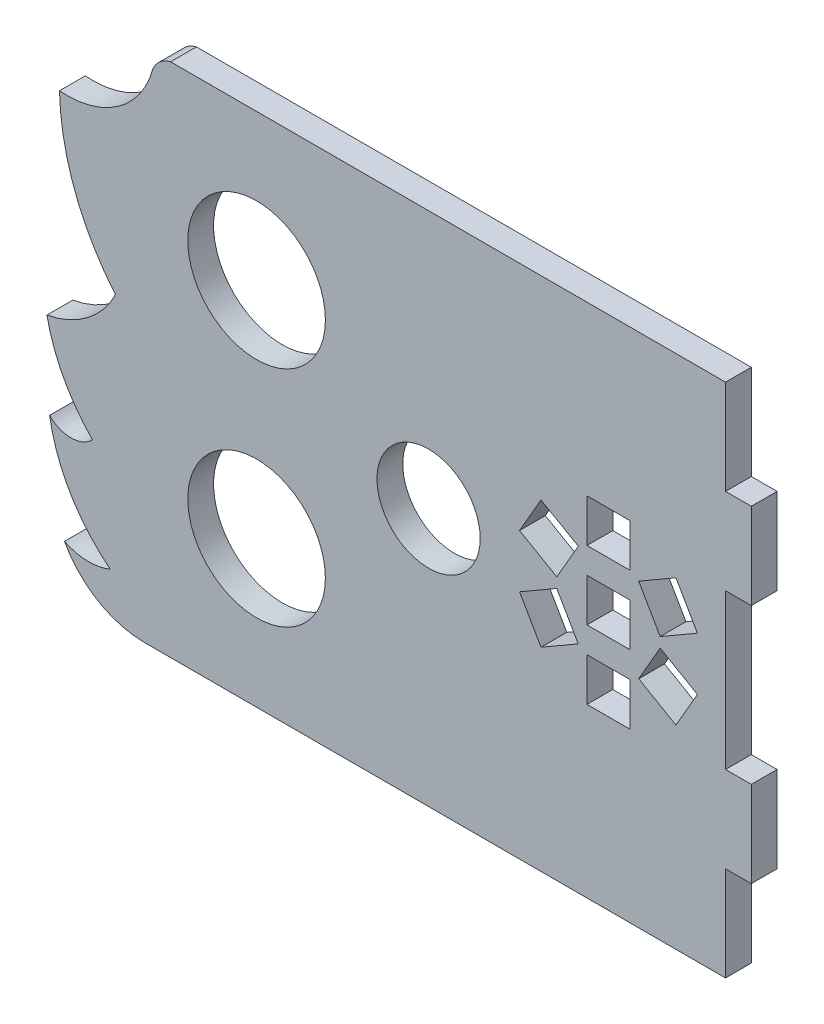
SolidWorks part; units mm, degrees
ref_plane "Alzado" through (0, 0, 0) normal (0, 0, 1) x (1, 0, 0)
ref_plane "Planta" through (0, 0, 0) normal (0, 1, 0) x (1, 0, 0)
ref_plane "Vista lateral" through (0, 0, 0) normal (1, 0, 0) x (0, 0, -1)
sketch "Model" plane through (0, 0, 0) normal (0, 0, 1) x (1, 0, 0)
  line L0 (76.3477, 34.88) -> (76.3477, 24.88)
  line L1 (76.3477, 6.88) -> (76.3477, -3.12)
  line L2 (53.7254, 16.4649) -> (56.2254, 20.7951)
  line L3 (49.3953, 18.9649) -> (53.7254, 16.4649)
  line L4 (51.8953, 23.2951) -> (49.3953, 18.9649)
  line L5 (56.2254, 20.7951) -> (51.8953, 23.2951)
  line L6 (49.3953, 12.7951) -> (51.8953, 8.4649)
  line L7 (53.7254, 15.2951) -> (49.3953, 12.7951)
  line L8 (56.2254, 10.9649) -> (53.7254, 15.2951)
  line L9 (51.8953, 8.4649) -> (56.2254, 10.9649)
  line L10 (62.2386, 26.38) -> (57.2386, 26.38)
  line L11 (62.2386, 21.38) -> (62.2386, 26.38)
  line L12 (57.2386, 21.38) -> (62.2386, 21.38)
  line L13 (57.2386, 26.38) -> (57.2386, 21.38)
  line L14 (65.7517, 15.2951) -> (63.2517, 10.9649)
  line L15 (70.0818, 12.7951) -> (65.7517, 15.2951)
  line L16 (67.5818, 8.4649) -> (70.0818, 12.7951)
  line L17 (63.2517, 10.9649) -> (67.5818, 8.4649)
  line L18 (70.0818, 18.9649) -> (67.5818, 23.2951)
  line L19 (65.7517, 16.4649) -> (70.0818, 18.9649)
  line L20 (63.2517, 20.7951) -> (65.7517, 16.4649)
  line L21 (67.5818, 23.2951) -> (63.2517, 20.7951)
  line L22 (62.2386, 10.38) -> (57.2386, 10.38)
  line L23 (62.2386, 5.38) -> (62.2386, 10.38)
  line L24 (57.2386, 5.38) -> (62.2386, 5.38)
  line L25 (57.2386, 10.38) -> (57.2386, 5.38)
  line L26 (62.2386, 18.38) -> (57.2386, 18.38)
  line L27 (62.2386, 13.38) -> (62.2386, 18.38)
  line L28 (57.2386, 13.38) -> (62.2386, 13.38)
  line L29 (57.2386, 18.38) -> (57.2386, 13.38)
  line L30 (5.8226, -14.12) -> (61.8276, -14.12)
  line L31 (11.313, 45.88) -> (8.8226, 45.88)
  line L32 (73.3477, -3.12) -> (76.3477, -3.12)
  line L33 (73.3477, -14.12) -> (73.3477, -3.12)
  line L34 (61.8276, -14.12) -> (73.3477, -14.12)
  line L35 (73.3477, 24.88) -> (76.3477, 24.88)
  line L36 (73.3477, 6.88) -> (73.3477, 24.88)
  line L37 (76.3477, 6.88) -> (73.3477, 6.88)
  line L38 (73.3477, 45.88) -> (11.313, 45.88)
  line L39 (73.3477, 34.88) -> (73.3477, 45.88)
  line L40 (76.3477, 34.88) -> (73.3477, 34.88)
  circle A0 centre (18.8226, 28.88) radius 8
  circle A1 centre (38.8226, 15.88) radius 6
  circle A2 centre (18.8226, 2.88) radius 8
  arc A3 (-3.5173, -8.5838) -> (5.8226, -14.12) centre (5.8215, -3.4753) ccw
  arc A4 (-3.5173, -8.5838) -> (1.8055, -8.7308) centre (-0.6916, -2.7088) ccw
  arc A5 (-5.2498, 3.2368) -> (1.8055, -8.7308) centre (13.8357, 6.4248) ccw
  arc A6 (-5.2498, 3.2368) -> (-0.2499, 3.2598) centre (-2.7614, 5.7483) ccw
  arc A7 (-5.5598, 13.1854) -> (-0.2499, 3.2598) centre (13.8348, 17.1779) ccw
  arc A8 (-5.5598, 13.1854) -> (2.4125, 19.2222) centre (-7.6105, 24.176) ccw
  arc A9 (-4.0953, 36.5028) -> (2.4125, 19.2222) centre (23.8281, 37.1529) ccw
  arc A10 (-4.0953, 36.5028) -> (6.7554, 44.1216) centre (-3.2058, 46.7721) ccw
  arc A11 (8.8226, 45.88) -> (6.7554, 44.1216) centre (9.5226, 42.9628) ccw
extrude "Saliente-Extruir1" add sketch "Model" along normal blind 3
